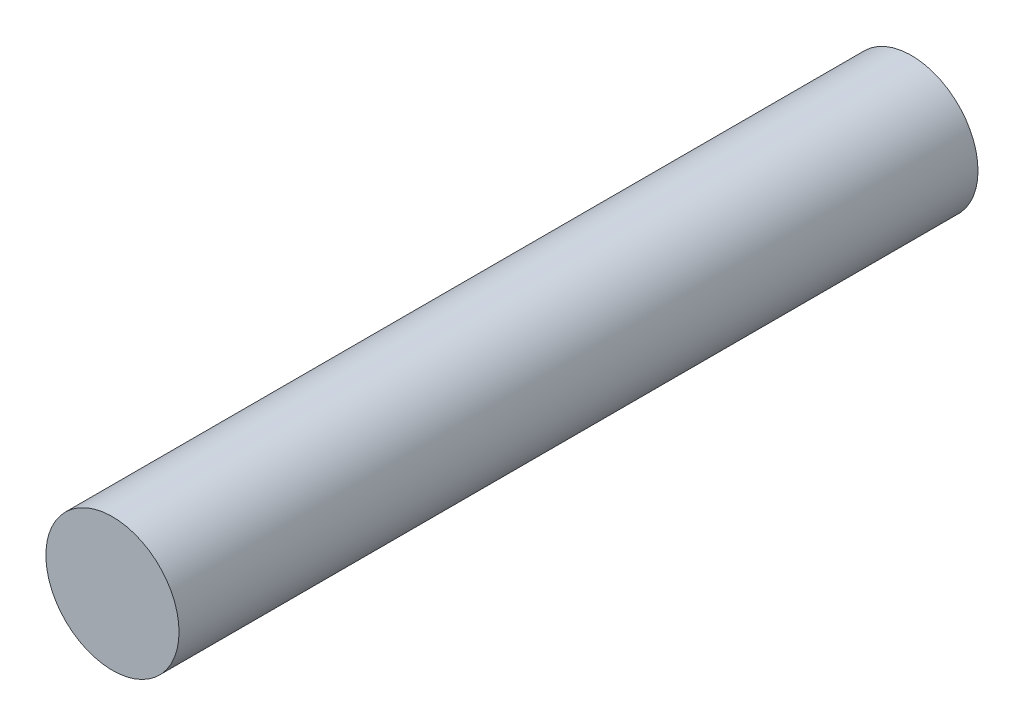
SolidWorks part; units mm, degrees
ref_plane "Front Plane" through (0, 0, 0) normal (0, 0, 1) x (1, 0, 0)
ref_plane "Top Plane" through (0, 0, 0) normal (0, 1, 0) x (1, 0, 0)
ref_plane "Right Plane" through (0, 0, 0) normal (1, 0, 0) x (0, 0, -1)
sketch "Sketch1" plane through (0, 0, 0) normal (0, 0, 1) x (1, 0, 0)
  circle A0 centre (0, 0) radius 3.75
  dimension "D1" = 7.5
extrude "Boss-Extrude1" add sketch "Sketch1" along normal blind 45
